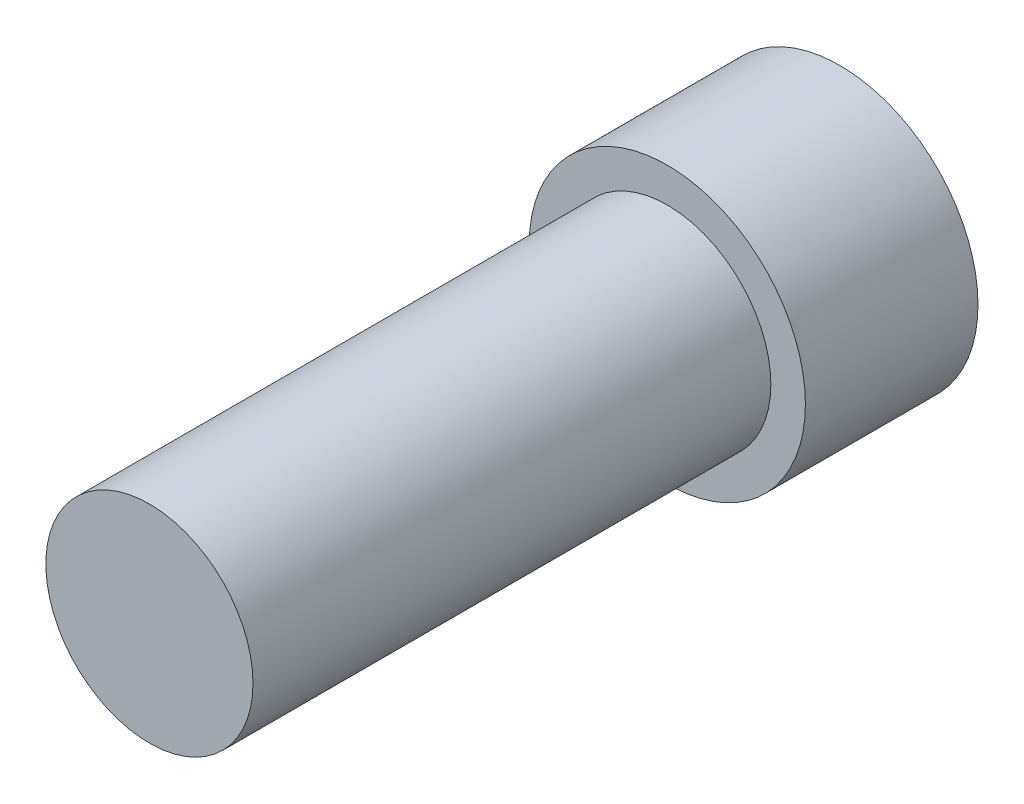
SolidWorks part; units mm, degrees
material "1023 Carbon Steel Sheet (SS)"
ref_plane "Front Plane" through (0, 0, 0) normal (0, 0, 1) x (1, 0, 0)
ref_plane "Top Plane" through (0, 0, 0) normal (0, 1, 0) x (1, 0, 0)
ref_plane "Right Plane" through (0, 0, 0) normal (1, 0, 0) x (0, 0, -1)
sketch "Sketch1" plane through (0, 0, 0) normal (0, 0, 1) x (1, 0, 0)
  circle A0 centre (0, 0) radius 4
extrude "Boss-Extrude1" add sketch "Sketch1" along normal blind 5
sketch "Sketch2" plane through (0, 0, 5) normal (0, 0, 1) x (1, 0, 0)
  circle A0 centre (0, 0) radius 3
extrude "Boss-Extrude2" add sketch "Sketch2" along normal blind 15
sketch "Sketch3" plane through (0, 0, 0) normal (0, 0, -1) x (-1, 0, 0)
  line L1 (0.2948, -2.7822) -> (2.5569, -1.1358)
  line L2 (2.5569, -1.1358) -> (2.2621, 1.6464)
  line L3 (2.2621, 1.6464) -> (-0.2948, 2.7822)
  line L4 (-0.2948, 2.7822) -> (-2.5569, 1.1358)
  line L5 (-2.5569, 1.1358) -> (-2.2621, -1.6464)
  line L6 (-2.2621, -1.6464) -> (0.2948, -2.7822)
  circle A0 centre (0, 0) radius 2.423 construction
extrude "Cut-Extrude1" cut sketch "Sketch3" against normal blind 3
